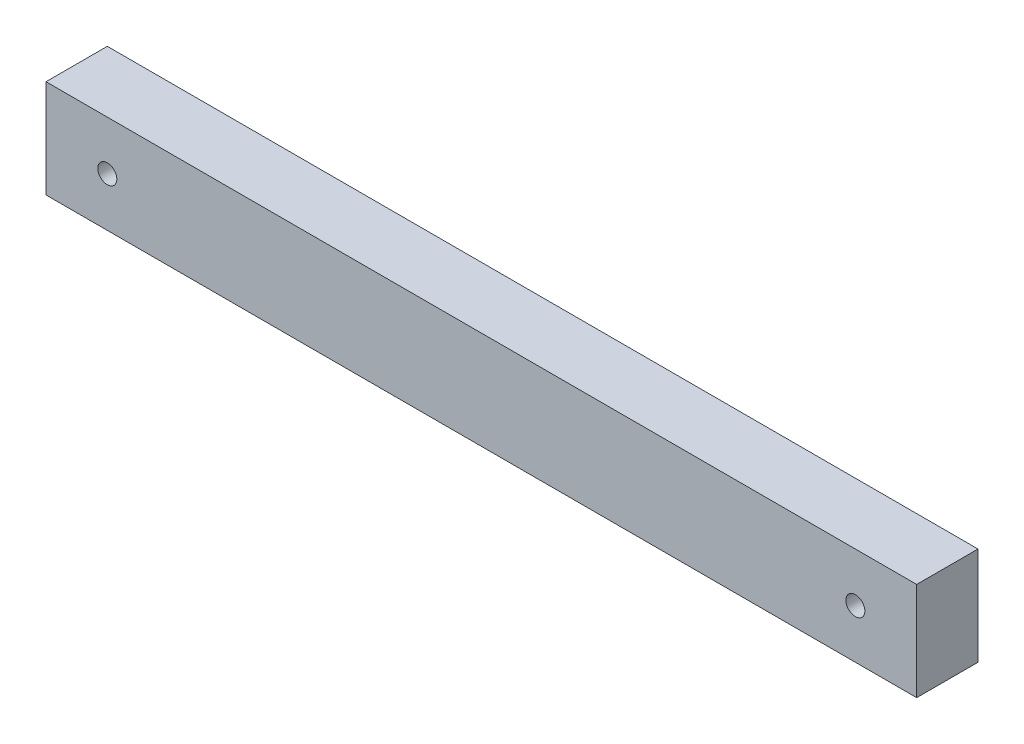
SolidWorks part; units mm, degrees
material "Carbon Sandwich"
ref_plane "Front Plane" through (0, 0, 0) normal (0, 0, 1) x (1, 0, 0)
ref_plane "Top Plane" through (0, 0, 0) normal (0, 1, 0) x (1, 0, 0)
ref_plane "Right Plane" through (0, 0, 0) normal (1, 0, 0) x (0, 0, -1)
sketch "Sketch1" plane through (0, 0, 0) normal (0, 0, 1) x (1, 0, 0)
  line L0 (0, 0) -> (50000, 0) construction
  line L1 (-71, -8) -> (71, -8)
  line L3 (-71, 8) -> (71, 8)
  line L5 (0, -8) -> (0, 8) construction
  line L6 (-71, 8) -> (-71, -8)
  line L8 (71, 8) -> (71, -8)
  circle A2 centre (61, 0) radius 1.55
  circle A4 centre (-61, 0) radius 1.55
  point P1 (-75, 0)
  point P3 (75, 0)
  dimension "D1" = 150
  dimension "D3" = 4
  dimension "D9" = 3.1
  dimension "D10" = 10
  dimension "D2" = 16
extrude "Boss-Extrude1" add sketch "Sketch1" along normal blind 10
